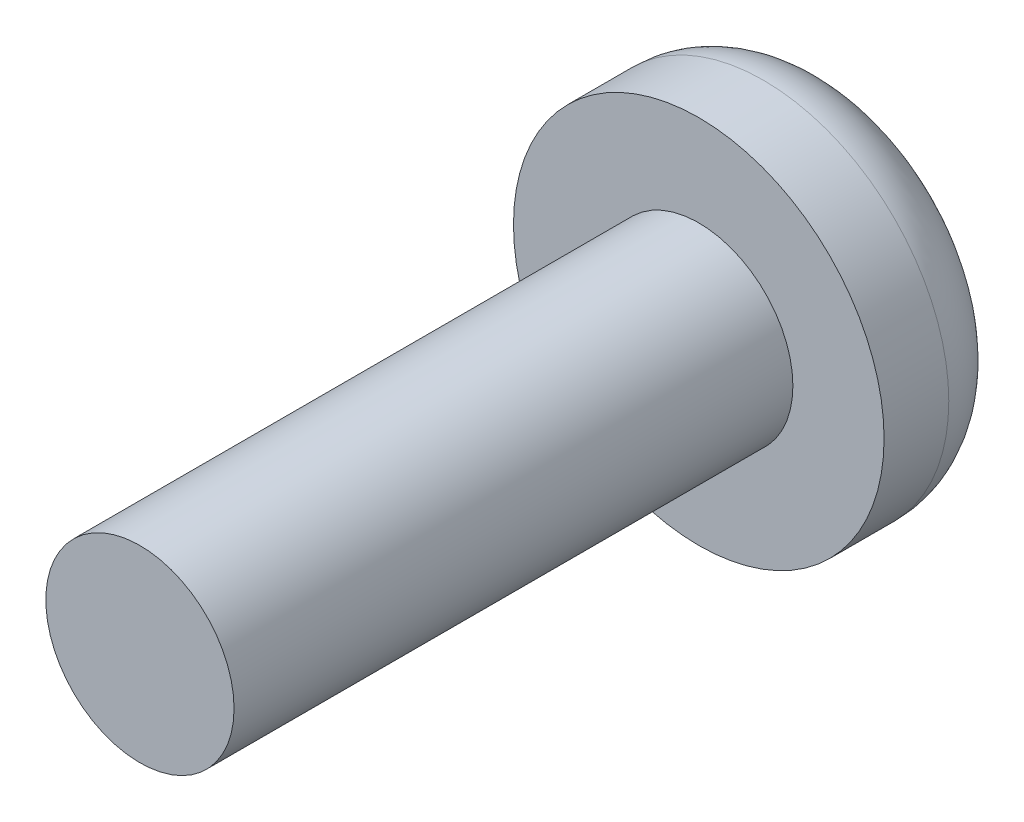
SolidWorks part; units mm, degrees
ref_plane "Front Plane" through (0, 0, 0) normal (0, 0, 1) x (1, 0, 0)
ref_plane "Top Plane" through (0, 0, 0) normal (0, 1, 0) x (1, 0, 0)
ref_plane "Right Plane" through (0, 0, 0) normal (1, 0, 0) x (0, 0, -1)
sketch "Sketch1" plane through (0, 0, 0) normal (0, 0, 1) x (1, 0, 0)
  circle A0 centre (0, 0) radius 4.0005
  dimension "D1" = 8.001
extrude "Extrude1" add sketch "Sketch1" along normal blind 2.921
fillet "Fillet1" radius 1.524 1 edges at (4.0005, 0, 0)
sketch "Sketch2" plane through (0, 0, 2.921) normal (0, 0, 1) x (1, 0, 0)
  circle A0 centre (0, 0) radius 2.032
extrude "Extrude2" add sketch "Sketch2" along normal blind 12.065
sketch "Sketch3" plane through (0, 0, 0) normal (0, 0, -1) x (-1, 0, 0)
  line L1 (2.4573, 0.3079) -> (-2.4573, 0.3079)
  line L2 (2.4573, 0.3079) -> (2.4573, -0.3079)
  line L3 (2.4573, -0.3079) -> (-2.4573, -0.3079)
  line L4 (-2.4573, 0.3079) -> (-2.4573, -0.3079)
  line L5 (2.4573, 0.3079) -> (-2.4573, -0.3079) construction
  line L6 (2.4573, -0.3079) -> (-2.4573, 0.3079) construction
  circle A0 centre (0, 0) radius 2.4765 construction
  point P0 (0, 0)
  point P8 (0, 0)
extrude "Extrude3" cut sketch "Sketch3" against normal blind 1.016
pattern_circular "CirPattern1" count 2 over 90 about axis through (0, 0, 0) along (0, 0, 1) of "Extrude3"
